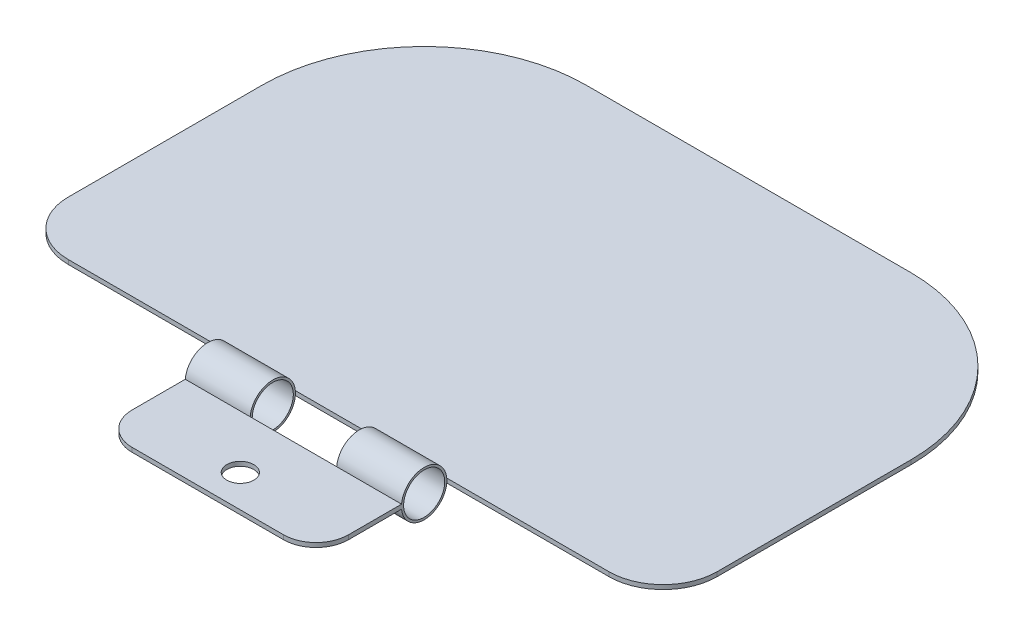
SolidWorks part; units mm, degrees
ref_plane "前视基准面" through (0, 0, 0) normal (0, 0, 1) x (1, 0, 0)
ref_plane "上视基准面" through (0, 0, 0) normal (0, 1, 0) x (1, 0, 0)
ref_plane "右视基准面" through (0, 0, 0) normal (1, 0, 0) x (0, 0, -1)
sketch "草图1" plane through (0, 0, 0) normal (1, 0, 0) x (0, 0, -1)
  line L1 (-10, -0.2) -> (-2.0905, -0.2)
  line L2 (-10, 0.2) -> (-2.0905, 0.2)
  line L3 (-10, 0.2) -> (-10, -0.2)
  line L4 (40, 0.2) -> (40, -0.2)
  line L5 (2.0905, 0.2) -> (40, 0.2)
  line L7 (2.0905, -0.2) -> (40, -0.2)
  arc A1 (2.0905, 0.2) -> (-2.0905, 0.2) centre (0, 0) ccw
  circle A2 centre (0, 0) radius 1.9
  arc A5 (-2.0905, -0.2) -> (2.0905, -0.2) centre (0, 0) ccw
extrude "凸台-拉伸1" add sketch "草图1" along normal blind 20
sketch "草图2" plane through (20, 0, 0) normal (1, 0, 0) x (0, 0, -1)
  line L0 (2.0905, -0.2) -> (2.0905, 0.2)
  line L1 (2.0905, 0.2) -> (40, 0.2)
  line L2 (40, 0.2) -> (40, -0.2)
  line L3 (40, -0.2) -> (2.0905, -0.2)
extrude "凸台-拉伸2" add sketch "草图2" along normal blind 20 and the other way blind 40
fillet "圆角1" radius 15 2 edges at (40, 0, -40) (-20, 0, -40)
fillet "圆角2" radius 5 2 edges at (40, 0, -2.0905) (-20, 0, -2.0905)
fillet "圆角3" radius 3 2 edges at (20, 0, 10) (0, 0, 10)
sketch "草图3" plane through (0, 0.2, 0) normal (0, 1, 0) x (1, 0, 0)
  line L0 (10, -2.0905) -> (10, -10)
  line L1 (20, -2.0905) -> (0, -2.0905) construction
  line L2 (17, -10) -> (3, -10) construction
  circle A0 centre (10, -7) radius 1.25
  dimension "D2" = 2.5
  dimension "D1" = 3
extrude "切除-拉伸1" cut sketch "草图3" against normal blind 20 contours L0 A0 | L0 A0
sketch "草图4" plane through (0, 0.2, 0) normal (0, 1, 0) x (1, 0, 0)
  line L0 (10, -10) -> (10, 5.0215) construction
  line L1 (17, -10) -> (3, -10) construction
  line L2 (0, 2.0905) -> (20, -2.0905) construction
  line L3 (20, -2.0905) -> (0, -2.0905) construction
  line L4 (6, 2.0905) -> (14, 2.0905)
  line L5 (6, 2.0905) -> (6, -2.0905)
  line L6 (6, -2.0905) -> (14, -2.0905)
  line L7 (14, 2.0905) -> (14, -2.0905)
  line L8 (6, 2.0905) -> (14, -2.0905) construction
  line L9 (6, -2.0905) -> (14, 2.0905) construction
  point P8 (10, 0)
  dimension "D1" = 8
extrude "切除-拉伸2" cut sketch "草图4" against normal through all and the other way through all
